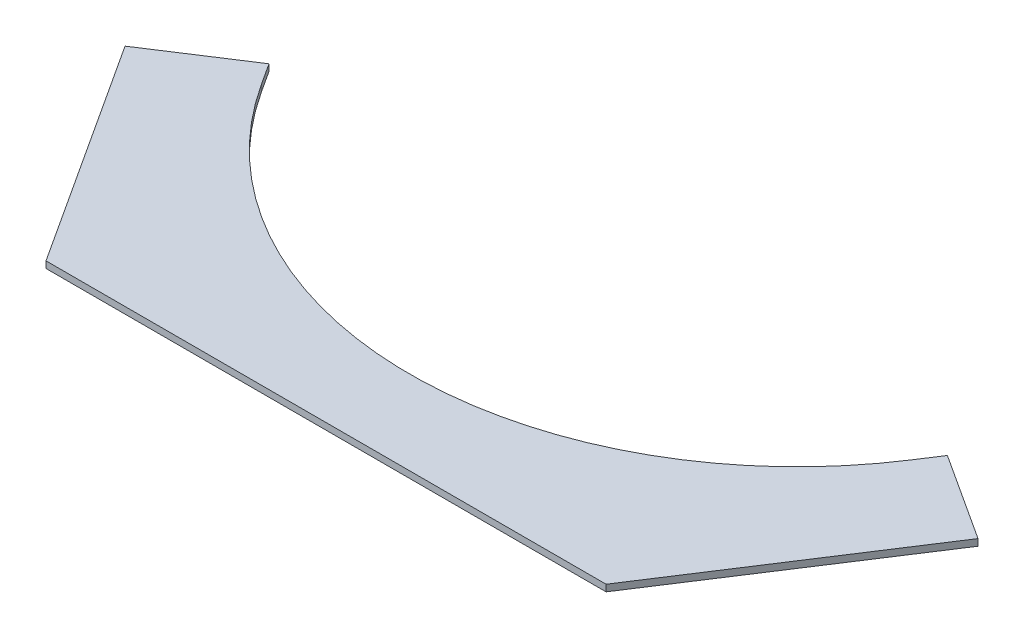
SolidWorks part; units mm, degrees
ref_plane "Front Plane" through (0, 0, 0) normal (0, 0, 1) x (1, 0, 0)
ref_plane "Top Plane" through (0, 0, 0) normal (0, 1, 0) x (1, 0, 0)
ref_plane "Right Plane" through (0, 0, 0) normal (1, 0, 0) x (0, 0, -1)
sketch "Sketch1" plane through (0, 0, 0) normal (0, 1, 0) x (1, 0, 0)
  line L0 (0, 0) -> (534.9068, 0)
  line L1 (674.7582, 215.3522) -> (534.9068, 0)
  line L2 (-139.8514, 215.3522) -> (0, 0)
  line L3 (674.7582, 215.3522) -> (591.4194, 269.4731)
  line L4 (-139.8514, 215.3522) -> (-56.5126, 269.4731)
  line L7 (-56.5126, 269.4731) -> (-42.8966, 248.5063)
  line L10 (591.4194, 269.4731) -> (577.8034, 248.5063)
  arc A0 (-42.8966, 248.5063) -> (577.8034, 248.5063) centre (267.4534, 450.05) ccw
extrude "Boss-Extrude1" add sketch "Sketch1" along normal blind 6.35
